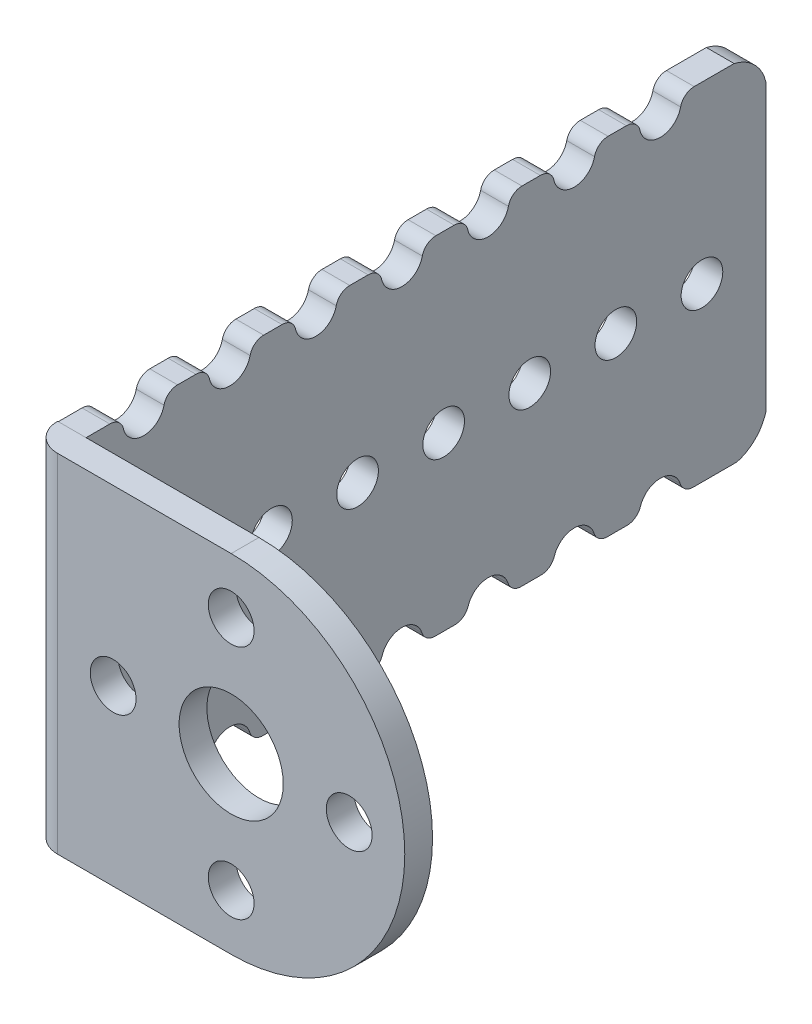
SolidWorks part; units mm, degrees
ref_plane "Alzado" through (0, 0, 0) normal (0, 0, 1) x (1, 0, 0)
ref_plane "Planta" through (0, 0, 0) normal (0, 1, 0) x (1, 0, 0)
ref_plane "Vista lateral" through (0, 0, 0) normal (1, 0, 0) x (0, 0, -1)
sketch "Croquis1" plane through (0, 0, 0) normal (0, 0, 1) x (1, 0, 0)
  line L0 (0, 0) -> (0, 25)
  line L1 (0, 0) -> (14.5, 0)
  line L2 (0, 25) -> (14.5, 25)
  line L3 (0, 12.5) -> (14.5, 12.5) construction
  line L4 (14.5, 12.5) -> (14.5, 25) construction
  line L5 (0, 12.5) -> (27, 12.5) construction
  circle A0 centre (14.5, 12.5) radius 3.75
  circle A1 centre (14.5, 21) radius 1.65
  circle A2 centre (23, 12.5) radius 1.65
  circle A3 centre (14.5, 4) radius 1.65
  circle A4 centre (6, 12.5) radius 1.65
  arc A5 (14.5, 25) -> (14.5, 0) centre (14.5, 12.5) cw
  dimension "D1" = 25
  dimension "D2" = 14.5
  dimension "D3" = 7.5
  dimension "D4" = 3.3
  dimension "D5" = 3.3
  dimension "D6" = 3.3
  dimension "D7" = 3.3
  dimension "D8" = 27
extrude "Saliente-Extruir1" add sketch "Croquis1" along normal blind 2
sketch "Croquis4" plane through (0, 0, 0) normal (-1, 0, 0) x (0, 0, 1)
  line L0 (-45.3169, 24.95) -> (-45.3169, 0) construction
  line L1 (2, 0) -> (-46.9228, 0)
  line L2 (2, 0) -> (2, 24.95)
  line L3 (2, 24.95) -> (-46.7155, 24.95)
  line L4 (-49, 2.0772) -> (-49, 22.6655)
  arc A0 (-46.7155, 24.95) -> (-49, 22.6655) centre (-46.0162, 21.9662) ccw
  arc A1 (-46.9228, 0) -> (-49, 2.0772) centre (-46.1199, 2.8801) cw
extrude "Saliente-Extruir2" add sketch "Croquis4" against normal blind 2
sketch "Croquis5" plane through (2, 0, 0) normal (1, 0, 0) x (0, 0, -1)
  line L0 (49, 12.3713) -> (44.4, 12.3713) construction
  line L1 (49, 22.6655) -> (49, 2.0772) construction
  line L2 (44.4, 12.3713) -> (38.2, 12.3713) construction
  line L3 (38.2, 12.3713) -> (32, 12.3713) construction
  line L4 (32, 12.3713) -> (25.8, 12.3713) construction
  line L5 (25.8, 12.3713) -> (19.6, 12.3713) construction
  line L6 (19.6, 12.3713) -> (13.4, 12.3713) construction
  line L7 (13.4, 12.3713) -> (7.2, 12.3713) construction
  line L8 (4.2, 24.5) -> (10.4, 24.5) construction
  line L11 (-2, 12.5) -> (-2, 24.5) construction
  line L12 (-2, 25) -> (-2, 0) construction
  line L13 (-2, 12.5) -> (-2, 0.5) construction
  line L14 (-2, 24.5) -> (4.2, 24.5) construction
  line L15 (10.4, 24.5) -> (16.6, 24.5) construction
  line L16 (16.6, 24.5) -> (22.8, 24.5) construction
  line L17 (22.8, 24.5) -> (29, 24.5) construction
  line L18 (29, 24.5) -> (35.2, 24.5) construction
  line L19 (35.2, 24.5) -> (41.4, 24.5) construction
  circle A0 centre (44.4, 12.3713) radius 1.5
  circle A1 centre (38.2, 12.3713) radius 1.5
  circle A2 centre (32, 12.3713) radius 1.5
  circle A3 centre (25.8, 12.3713) radius 1.5
  circle A4 centre (19.6, 12.3713) radius 1.5
  circle A5 centre (13.4, 12.3713) radius 1.5
  circle A6 centre (7.2, 12.3713) radius 1.5
  circle A7 centre (4.2, 24.5) radius 1.5
  circle A8 centre (10.4, 24.5) radius 1.5
  circle A9 centre (16.6, 24.5) radius 1.5
  circle A10 centre (22.8, 24.5) radius 1.5
  circle A11 centre (29, 24.5) radius 1.5
  circle A12 centre (35.2, 24.5) radius 1.5
  circle A13 centre (41.4, 24.5) radius 1.5
  circle A15 centre (41.4, 0.2427) radius 1.5
  circle A16 centre (35.2, 0.2427) radius 1.5
  circle A17 centre (29, 0.2427) radius 1.5
  circle A18 centre (22.8, 0.2427) radius 1.5
  circle A19 centre (16.6, 0.2427) radius 1.5
  circle A20 centre (10.4, 0.2427) radius 1.5
  circle A21 centre (4.2, 0.2427) radius 1.5
  dimension "D2" = 3
  dimension "D4" = 6.2
  dimension "D6" = 3
  dimension "D7" = 3
  dimension "D8" = 3
  dimension "D12" = 3
  dimension "D13" = 3
  dimension "D14" = 3
  dimension "D18" = 3
  dimension "D20" = 3
  dimension "D23" = 6.2
  dimension "D25" = 3
  dimension "D26" = 3
  dimension "D27" = 3
  dimension "D28" = 3
  dimension "D29" = 3
  dimension "D1" = 4.6
  dimension "D3" = 6.2
  dimension "D5" = 6.2
  dimension "D9" = 6.2
  dimension "D10" = 6.2
  dimension "D11" = 6.2
  dimension "D15" = 6.2
  dimension "D16" = 12
  dimension "D17" = 12
  dimension "D19" = 6.2
  dimension "D21" = 6.2
  dimension "D22" = 6.2
  dimension "D24" = 6.2
  dimension "D30" = 6.2
extrude "Cortar-Extruir2" cut sketch "Croquis5" against normal blind 10
fillet "Redondeo3" radius 1 2 edges at (1, 24.95, -8.9691) (1, 24.95, -5.6309)
fillet "Redondeo4" radius 1 4 edges at (1, 24.95, -21.3691) (1, 24.95, -15.1691) (1, 24.95, -18.0309) (1, 24.95, -11.8309)
fillet "Redondeo5" radius 1 7 edges at (1, 24.95, -39.9691) (1, 24.95, -42.8309) (1, 24.95, -33.7691) (1, 24.95, -36.6309) (1, 24.95, -27.5691) (1, 24.95, -30.4309) (1, 24.95, -24.2309)
fillet "Redondeo6" radius 1 1 edges at (1, 24.95, -2.7691)
fillet "Redondeo7" radius 1 9 edges at (1, 0, -27.5198) (1, 0, -24.2802) (1, 0, -21.3198) (1, 0, -18.0802) (1, 0, -15.1198) (1, 0, -11.8802) (1, 0, -8.9198) (1, 0, -5.6802) (1, 0, -2.7198)
fillet "Redondeo8" radius 1 5 edges at (1, 0, -42.8802) (1, 0, -39.9198) (1, 0, -36.6802) (1, 0, -33.7198) (1, 0, -30.4802)
fillet "Redondeo12" radius 2 1 edges at (0, 12.5, 2)
